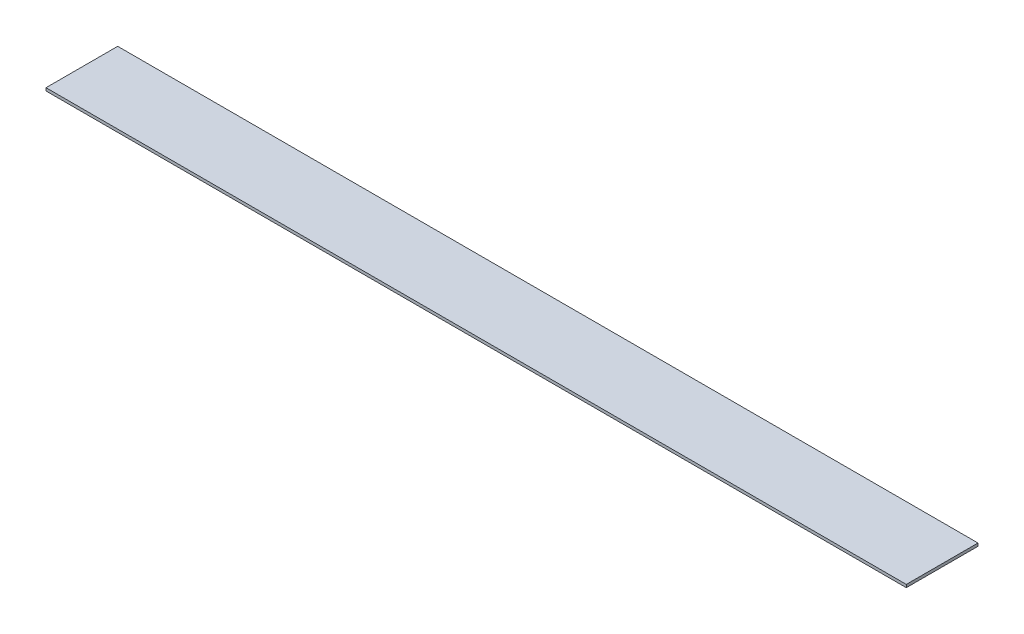
SolidWorks part; units mm, degrees
material "1023 Carbon Steel Sheet (SS)"
ref_plane "Front Plane" through (0, 0, 0) normal (0, 0, 1) x (1, 0, 0)
ref_plane "Top Plane" through (0, 0, 0) normal (0, 1, 0) x (1, 0, 0)
ref_plane "Right Plane" through (0, 0, 0) normal (1, 0, 0) x (0, 0, -1)
sketch "Sketch1" plane through (0, 0, 0) normal (0, 1, 0) x (1, 0, 0)
  line L1 (-150, 12.5) -> (150, 12.5)
  line L2 (-150, 12.5) -> (-150, -12.5)
  line L3 (-150, -12.5) -> (150, -12.5)
  line L4 (150, 12.5) -> (150, -12.5)
  line L5 (-150, 12.5) -> (150, -12.5) construction
  line L6 (-150, -12.5) -> (150, 12.5) construction
  point P0 (0, 0)
  dimension "D1" = 25
  dimension "D2" = 300
extrude "Boss-Extrude1" add sketch "Sketch1" along normal blind 1
